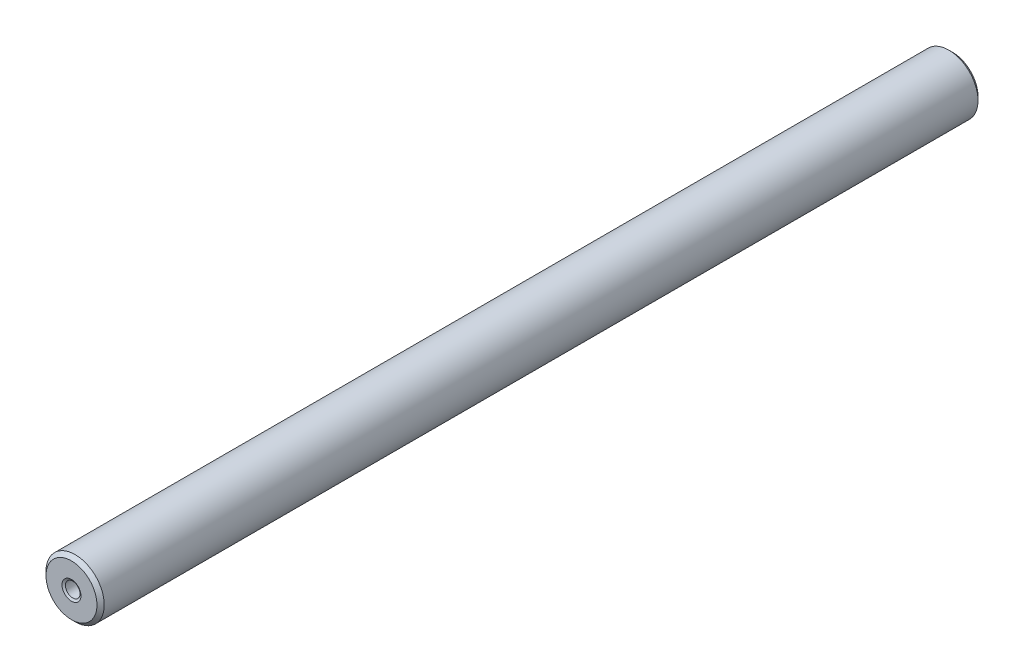
SolidWorks part; units mm, degrees
ref_plane "Front Plane" through (0, 0, 0) normal (0, 0, 1) x (1, 0, 0)
ref_plane "Top Plane" through (0, 0, 0) normal (0, 1, 0) x (1, 0, 0)
ref_plane "Right Plane" through (0, 0, 0) normal (1, 0, 0) x (0, 0, -1)
sketch "Sketch1" plane through (0, 0, 0) normal (0, 1, 0) x (1, 0, 0)
  line L0 (0, 0) -> (0, -121) construction
  line L1 (0, 0) -> (-4, 0) construction
  line L2 (-4, 0) -> (-4, -121) construction
  line L3 (-4, -121) -> (0, -121) construction
  line L4 (-1, 0) -> (-1, -121) construction
  line L5 (0, -2) -> (-4, -2) construction
  line L6 (-1, 0) -> (-4, 0)
  line L7 (0, -60.5) -> (-4, -60.5) construction
  line L8 (0, -2) -> (-1, -2)
  line L9 (-1, -2) -> (-1, 0)
  line L10 (0, -119) -> (-1, -119)
  line L11 (-1, -119) -> (-1, -121)
  line L12 (-4, 0) -> (-4, -121)
  line L13 (-4, -121) -> (-1, -121)
  line L14 (0, -119) -> (0, -2)
  dimension "D1" = 121
  dimension "D2" = 4
  dimension "D3" = 1
  dimension "D4" = 2
revolve "Revolve1" add sketch "Sketch1" angle 360 about L14
chamfer "Chamfer1" distance 0.5 angle 45 2 edges at (4, 0, 0) (4, 0, 121)
chamfer "Chamfer2" distance 0.3 angle 30 4 edges at (1, 0, 2) (1, 0, 0) (1, 0, 119) (1, 0, 121)
